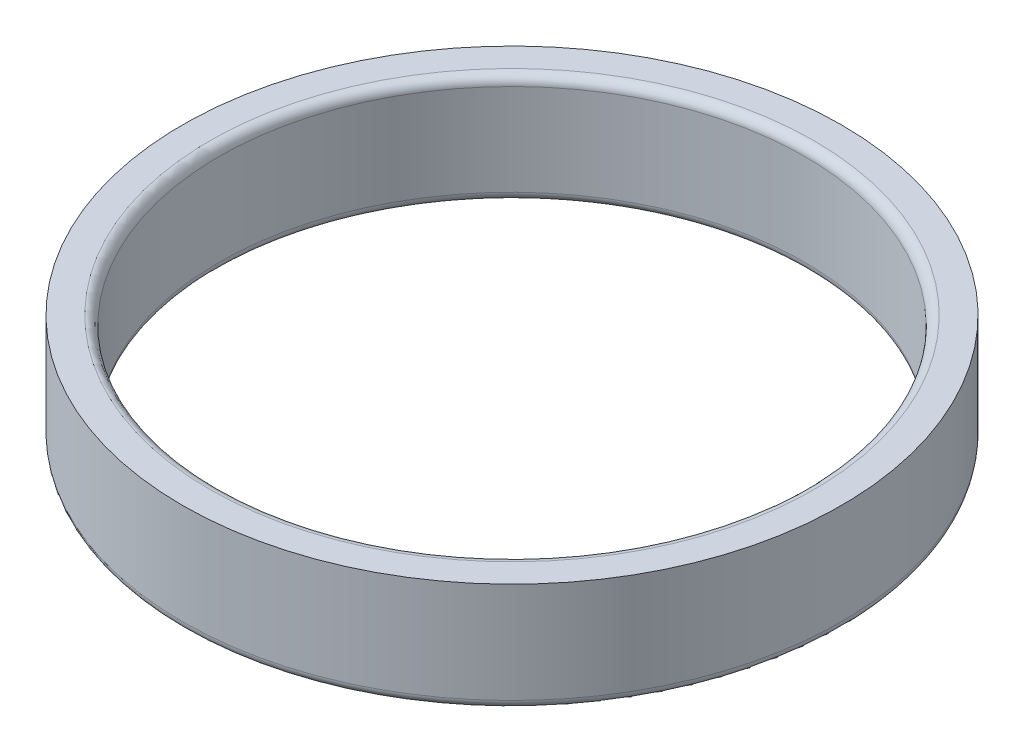
SolidWorks part; units mm, degrees
material "硅橡胶"
ref_plane "前视基准面" through (0, 0, 0) normal (0, 0, 1) x (1, 0, 0)
ref_plane "上视基准面" through (0, 0, 0) normal (0, 1, 0) x (1, 0, 0)
ref_plane "右视基准面" through (0, 0, 0) normal (1, 0, 0) x (0, 0, -1)
sketch "草图1" plane through (0, 0, 0) normal (0, 1, 0) x (1, 0, 0)
  circle A0 centre (0, 0) radius 8
  circle A1 centre (0, 0) radius 9
  dimension "D1" = 16
  dimension "D2" = 18
extrude "凸台-拉伸1" add sketch "草图1" along normal blind 3
fillet "圆角1" radius 0.25 3 edges at (0, 3, 8) (0, 0, 8) (0, 0, 9)
